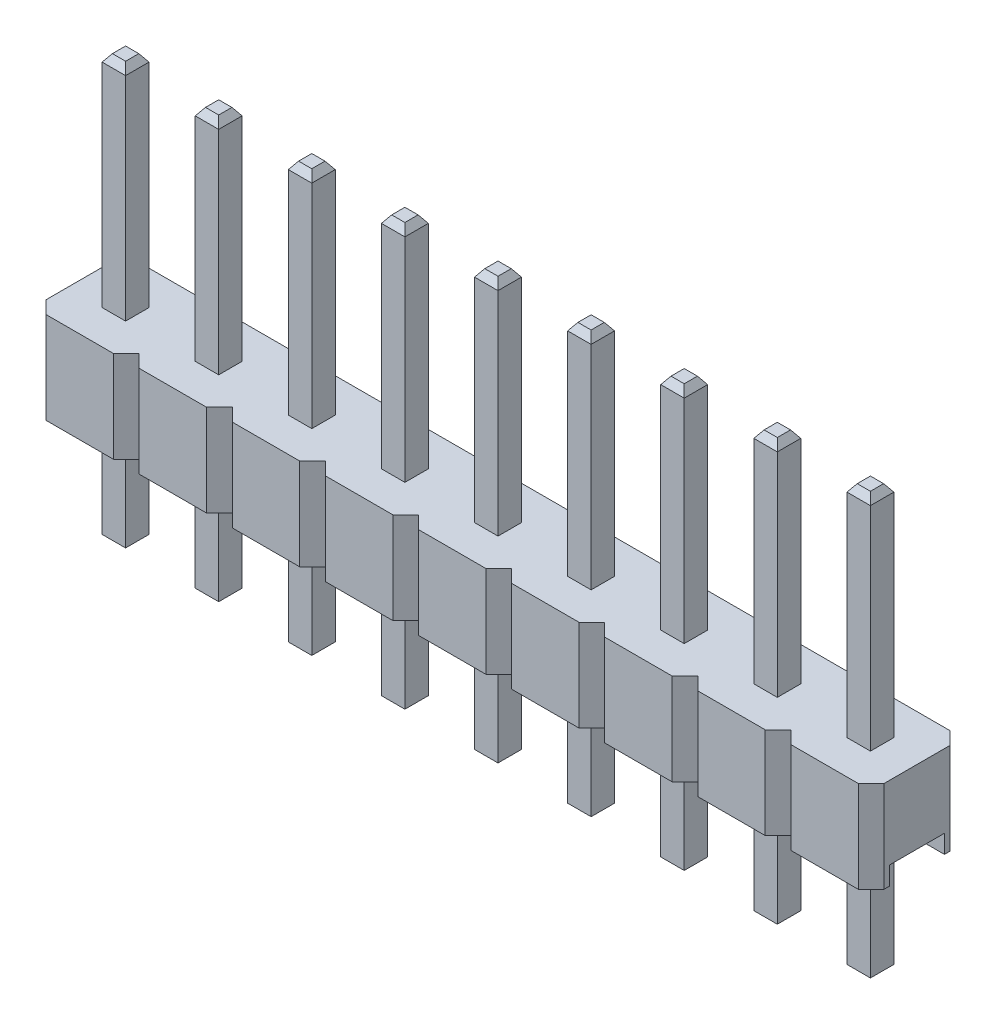
SolidWorks part; units mm, degrees
ref_plane "Front Plane" through (0, 0, 0) normal (0, 0, 1) x (1, 0, 0)
ref_plane "Top Plane" through (0, 0, 0) normal (0, 1, 0) x (1, 0, 0)
ref_plane "Right Plane" through (0, 0, 0) normal (1, 0, 0) x (0, 0, -1)
sketch "Sketch1" plane through (0, 0, 0) normal (0, 1, 0) x (1, 0, 0)
  line L0 (0, 2.15) -> (0.35, 2.5)
  line L1 (0.35, 0) -> (2.19, 0)
  line L2 (0, 0.35) -> (0, 2.15)
  line L3 (0.35, 2.5) -> (2.19, 2.5)
  line L4 (2.54, 0.35) -> (2.54, 2.15)
  line L5 (2.19, 2.5) -> (2.54, 2.15)
  line L6 (2.19, 0) -> (2.54, 0.35)
  line L7 (0, 0.35) -> (0.35, 0)
  point P0 (0, 0)
  point P1 (2.54, 2.5)
  point P2 (0, 2.5)
  point P3 (2.54, 0)
  dimension "D1" = 2.5
  dimension "D2" = 2.54
extrude "Boss-Extrude1" add sketch "Sketch1" along normal blind 2.5
sketch "Sketch3" plane through (0, 0, 0) normal (0, -1, 0) x (1, 0, 0)
  line L0 (0, -1.25) -> (2.54, -1.25) construction
  line L1 (0, -2.15) -> (0, -0.35) construction
  line L2 (2.54, -0.35) -> (2.54, -2.15) construction
  line L4 (0, -2) -> (2.54, -2)
  line L5 (0, -2) -> (0, -0.5)
  line L6 (0, -0.5) -> (2.54, -0.5)
  line L7 (2.54, -2) -> (2.54, -0.5)
  line L8 (0, -2) -> (2.54, -0.5) construction
  line L9 (0, -0.5) -> (2.54, -2) construction
  point P6 (1.27, -1.25)
  dimension "D1" = 1.5
extrude "Cut-Extrude1" cut sketch "Sketch3" against normal blind 0.5
sketch "Sketch4" plane through (0, 2.5, 0) normal (0, 1, 0) x (1, 0, 0)
  line L0 (0, 1.25) -> (2.54, 1.25) construction
  line L1 (0, 2.15) -> (0, 0.35) construction
  line L2 (2.54, 0.35) -> (2.54, 2.15) construction
  line L4 (0.95, 0.93) -> (1.59, 0.93)
  line L5 (0.95, 0.93) -> (0.95, 1.57)
  line L6 (0.95, 1.57) -> (1.59, 1.57)
  line L7 (1.59, 0.93) -> (1.59, 1.57)
  line L8 (0.95, 0.93) -> (1.59, 1.57) construction
  line L9 (0.95, 1.57) -> (1.59, 0.93) construction
  point P6 (1.27, 1.25)
  dimension "D1" = 0.64
extrude "Boss-Extrude2" add sketch "Sketch4" along normal blind 6 and the other way blind 5.5
chamfer "Chamfer1" distance 0.2 angle 35 8 edges at (1.27, -3, -1.57) (0.95, -3, -1.25) (1.27, -3, -0.93) (1.59, -3, -1.25) (1.27, 8.5, -0.93) (0.95, 8.5, -1.25) (1.27, 8.5, -1.57) (1.59, 8.5, -1.25)
pattern_linear "LPattern3" count 9 spacing 2.54 along (-1, 0, 0) of "Boss-Extrude1", "Cut-Extrude1", "Boss-Extrude2", "Chamfer1"
